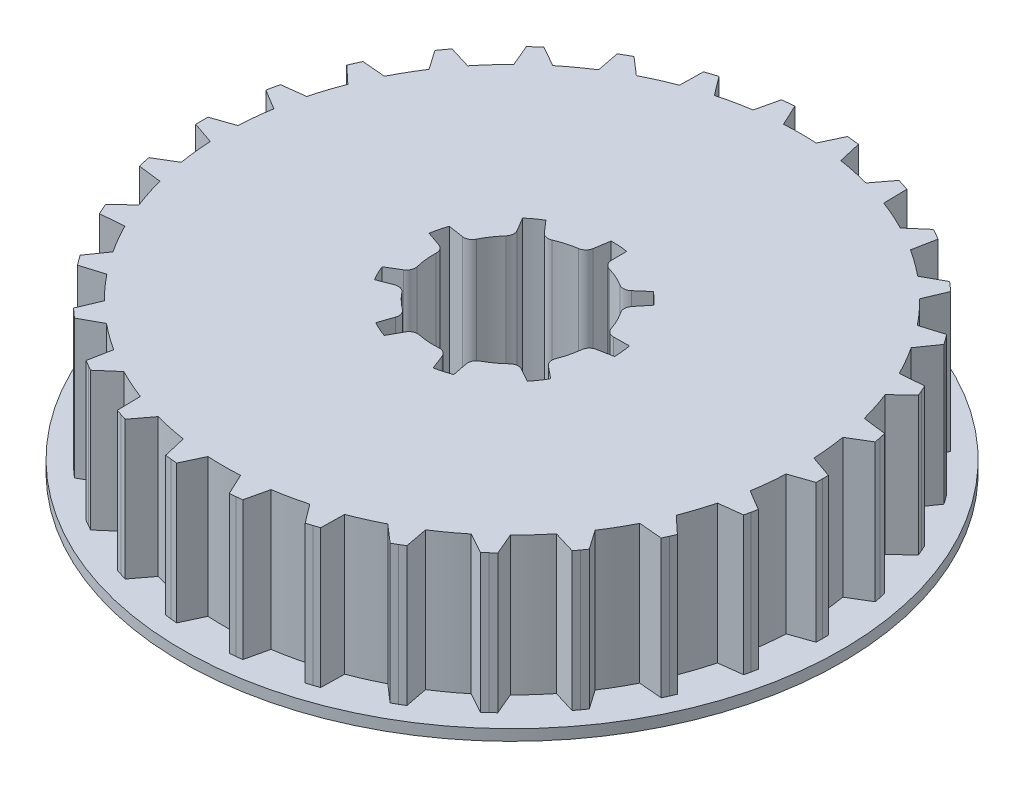
SolidWorks part; units mm, degrees
ref_plane "Front Plane" through (0, 0, 0) normal (0, 0, 1) x (1, 0, 0)
ref_plane "Top Plane" through (0, 0, 0) normal (0, 1, 0) x (1, 0, 0)
ref_plane "Right Plane" through (0, 0, 0) normal (1, 0, 0) x (0, 0, -1)
sketch "Sketch1" plane through (0, 0, 0) normal (0, 1, 0) x (1, 0, 0)
  circle A0 centre (0, 0) radius 13.12
  dimension "D1" = 26.24
extrude "Boss-Extrude1" add sketch "Sketch1" along normal blind 6.3
sketch "Sketch2" plane through (0, 0, 0) normal (0, -1, 0) x (1, 0, 0)
  line L0 (0, 0) -> (-14.12, 0) construction
  line L1 (-13.1243, 0) -> (-13.1049, -0.6297) construction
  line L2 (-13.1243, 0) -> (-13.1049, 0.6297) construction
  line L3 (-14.12, 0) -> (-14.1172, -0.28)
  line L4 (-14.12, 0) -> (-14.1172, 0.28)
  line L5 (-14.1172, -0.28) -> (-12.5942, -0.8061)
  line L6 (-14.1172, 0.28) -> (-12.5942, 0.8061)
  line L7 (-13.8669, 2.6613) -> (-12.4866, 1.83)
  line L8 (-13.7505, 3.209) -> (-12.1514, 3.407)
  line L9 (-13.8114, 2.9357) -> (-13.8669, 2.6613)
  line L10 (-13.8114, 2.9357) -> (-13.7505, 3.209)
  line L11 (-13.0106, 5.4862) -> (-11.8333, 4.3861)
  line L12 (-12.7828, 5.9978) -> (-11.1775, 5.8589)
  line L13 (-12.8993, 5.7431) -> (-13.0106, 5.4862)
  line L14 (-12.8993, 5.7431) -> (-12.7828, 5.9978)
  line L15 (-11.5856, 8.0714) -> (-10.6628, 6.7505)
  line L16 (-11.2565, 8.5244) -> (-9.7151, 8.0548)
  line L17 (-11.4233, 8.2995) -> (-11.5856, 8.0714)
  line L18 (-11.4233, 8.2995) -> (-11.2565, 8.5244)
  line L19 (-9.6543, 10.3038) -> (-9.0262, 8.8199)
  line L20 (-9.2382, 10.6785) -> (-7.8281, 9.8987)
  line L21 (-9.4481, 10.4932) -> (-9.6543, 10.3038)
  line L22 (-9.4481, 10.4932) -> (-9.2382, 10.6785)
  line L23 (-7.3011, 12.0859) -> (-6.9952, 10.5039)
  line L24 (-6.8161, 12.3659) -> (-5.599, 11.31)
  line L25 (-7.06, 12.2283) -> (-7.3011, 12.0859)
  line L26 (-7.06, 12.2283) -> (-6.8161, 12.3659)
  line L27 (-4.6287, 13.3398) -> (-4.6585, 11.7287)
  line L28 (-4.0962, 13.5128) -> (-3.1252, 12.2269)
  line L29 (-4.3633, 13.4289) -> (-4.6287, 13.3398)
  line L30 (-4.3633, 13.4289) -> (-4.0962, 13.5128)
  line L31 (-1.7541, 14.0106) -> (-2.1181, 12.441)
  line L32 (-1.1972, 14.0692) -> (-0.5148, 12.6095)
  line L33 (-1.4759, 14.0426) -> (-1.7541, 14.0106)
  line L34 (-1.4759, 14.0426) -> (-1.1972, 14.0692)
  line L35 (1.1972, 14.0692) -> (0.5148, 12.6095)
  line L36 (1.7541, 14.0106) -> (2.1181, 12.441)
  line L37 (1.4759, 14.0426) -> (1.1972, 14.0692)
  line L38 (1.4759, 14.0426) -> (1.7541, 14.0106)
  line L39 (4.0962, 13.5128) -> (3.1252, 12.2269)
  line L40 (4.6288, 13.3398) -> (4.6585, 11.7287)
  line L41 (4.3633, 13.4289) -> (4.0962, 13.5128)
  line L42 (4.3633, 13.4289) -> (4.6288, 13.3398)
  line L43 (6.8161, 12.3659) -> (5.599, 11.31)
  line L44 (7.3011, 12.0859) -> (6.9952, 10.5039)
  line L45 (7.06, 12.2283) -> (6.8161, 12.3659)
  line L46 (7.06, 12.2283) -> (7.3011, 12.0859)
  line L47 (9.2382, 10.6785) -> (7.8281, 9.8987)
  line L48 (9.6543, 10.3038) -> (9.0262, 8.82)
  line L49 (9.4481, 10.4932) -> (9.2382, 10.6785)
  line L50 (9.4481, 10.4932) -> (9.6543, 10.3038)
  line L51 (11.2565, 8.5244) -> (9.7151, 8.0549)
  line L52 (11.5857, 8.0714) -> (10.6628, 6.7506)
  line L53 (11.4233, 8.2995) -> (11.2565, 8.5244)
  line L54 (11.4233, 8.2995) -> (11.5857, 8.0714)
  line L55 (12.7828, 5.9978) -> (11.1775, 5.8589)
  line L56 (13.0106, 5.4862) -> (11.8333, 4.3861)
  line L57 (12.8993, 5.7431) -> (12.7828, 5.9978)
  line L58 (12.8993, 5.7431) -> (13.0106, 5.4862)
  line L59 (13.7505, 3.209) -> (12.1514, 3.407)
  line L60 (13.8669, 2.6613) -> (12.4866, 1.83)
  line L61 (13.8114, 2.9357) -> (13.7505, 3.209)
  line L62 (13.8114, 2.9357) -> (13.8669, 2.6613)
  line L63 (14.1172, 0.28) -> (12.5942, 0.8061)
  line L64 (14.1172, -0.28) -> (12.5942, -0.8061)
  line L65 (14.12, 0) -> (14.1172, 0.28)
  line L66 (14.12, 0) -> (14.1172, -0.28)
  line L67 (13.8669, -2.6613) -> (12.4866, -1.83)
  line L68 (13.7505, -3.209) -> (12.1514, -3.407)
  line L69 (13.8114, -2.9357) -> (13.8669, -2.6613)
  line L70 (13.8114, -2.9357) -> (13.7505, -3.209)
  line L71 (13.0106, -5.4862) -> (11.8333, -4.3861)
  line L72 (12.7828, -5.9978) -> (11.1775, -5.8589)
  line L73 (12.8993, -5.7431) -> (13.0106, -5.4862)
  line L74 (12.8993, -5.7431) -> (12.7828, -5.9978)
  line L75 (11.5856, -8.0714) -> (10.6628, -6.7505)
  line L76 (11.2565, -8.5244) -> (9.7151, -8.0548)
  line L77 (11.4233, -8.2995) -> (11.5856, -8.0714)
  line L78 (11.4233, -8.2995) -> (11.2565, -8.5244)
  line L79 (9.6543, -10.3038) -> (9.0262, -8.8199)
  line L80 (9.2382, -10.6785) -> (7.8281, -9.8987)
  line L81 (9.4481, -10.4932) -> (9.6543, -10.3038)
  line L82 (9.4481, -10.4932) -> (9.2382, -10.6785)
  line L83 (7.3011, -12.0859) -> (6.9952, -10.5039)
  line L84 (6.8161, -12.3659) -> (5.599, -11.31)
  line L85 (7.06, -12.2283) -> (7.3011, -12.0859)
  line L86 (7.06, -12.2283) -> (6.8161, -12.3659)
  line L87 (4.6287, -13.3398) -> (4.6585, -11.7287)
  line L88 (4.0962, -13.5128) -> (3.1252, -12.2269)
  line L89 (4.3633, -13.4289) -> (4.6287, -13.3398)
  line L90 (4.3633, -13.4289) -> (4.0962, -13.5128)
  line L91 (1.7541, -14.0106) -> (2.1181, -12.441)
  line L92 (1.1972, -14.0692) -> (0.5148, -12.6095)
  line L93 (1.4759, -14.0426) -> (1.7541, -14.0106)
  line L94 (1.4759, -14.0426) -> (1.1972, -14.0692)
  line L95 (-1.1972, -14.0692) -> (-0.5148, -12.6095)
  line L96 (-1.7541, -14.0106) -> (-2.1181, -12.441)
  line L97 (-1.4759, -14.0426) -> (-1.1972, -14.0692)
  line L98 (-1.4759, -14.0426) -> (-1.7541, -14.0106)
  line L99 (-4.0962, -13.5128) -> (-3.1252, -12.2269)
  line L100 (-4.6288, -13.3398) -> (-4.6585, -11.7287)
  line L101 (-4.3633, -13.4289) -> (-4.0962, -13.5128)
  line L102 (-4.3633, -13.4289) -> (-4.6288, -13.3398)
  line L103 (-6.8161, -12.3659) -> (-5.599, -11.31)
  line L104 (-7.3011, -12.0859) -> (-6.9952, -10.5039)
  line L105 (-7.06, -12.2283) -> (-6.8161, -12.3659)
  line L106 (-7.06, -12.2283) -> (-7.3011, -12.0859)
  line L107 (-9.2382, -10.6785) -> (-7.8281, -9.8987)
  line L108 (-9.6543, -10.3038) -> (-9.0262, -8.82)
  line L109 (-9.4481, -10.4932) -> (-9.2382, -10.6785)
  line L110 (-9.4481, -10.4932) -> (-9.6543, -10.3038)
  line L111 (-11.2565, -8.5244) -> (-9.7151, -8.0549)
  line L112 (-11.5857, -8.0714) -> (-10.6628, -6.7506)
  line L113 (-11.4233, -8.2995) -> (-11.2565, -8.5244)
  line L114 (-11.4233, -8.2995) -> (-11.5857, -8.0714)
  line L115 (-12.7828, -5.9978) -> (-11.1775, -5.8589)
  line L116 (-13.0106, -5.4862) -> (-11.8333, -4.3861)
  line L117 (-12.8993, -5.7431) -> (-12.7828, -5.9978)
  line L118 (-12.8993, -5.7431) -> (-13.0106, -5.4862)
  line L119 (-13.7505, -3.209) -> (-12.1514, -3.407)
  line L120 (-13.8669, -2.6613) -> (-12.4866, -1.83)
  line L121 (-13.8114, -2.9357) -> (-13.7505, -3.209)
  line L122 (-13.8114, -2.9357) -> (-13.8669, -2.6613)
  circle A0 centre (0, 0) radius 13.12 construction
  arc A1 (-12.5942, 0.8061) -> (-12.5942, -0.8061) centre (0, 0) ccw
  arc A2 (-12.1514, 3.407) -> (-12.4866, 1.83) centre (0, 0) ccw
  arc A4 (-11.1775, 5.8589) -> (-11.8333, 4.3861) centre (0, 0) ccw
  arc A6 (-9.7151, 8.0548) -> (-10.6628, 6.7505) centre (0, 0) ccw
  arc A7 (-7.8281, 9.8987) -> (-9.0262, 8.8199) centre (0, 0) ccw
  arc A8 (-5.599, 11.31) -> (-6.9952, 10.5039) centre (0, 0) ccw
  arc A9 (-3.1252, 12.2269) -> (-4.6585, 11.7287) centre (0, 0) ccw
  arc A10 (-0.5148, 12.6095) -> (-2.1181, 12.441) centre (0, 0) ccw
  arc A11 (2.1181, 12.441) -> (0.5148, 12.6095) centre (0, 0) ccw
  arc A12 (4.6585, 11.7287) -> (3.1252, 12.2269) centre (0, 0) ccw
  arc A13 (6.9952, 10.5039) -> (5.599, 11.31) centre (0, 0) ccw
  arc A14 (9.0262, 8.82) -> (7.8281, 9.8987) centre (0, 0) ccw
  arc A15 (10.6628, 6.7506) -> (9.7151, 8.0549) centre (0, 0) ccw
  arc A16 (11.8333, 4.3861) -> (11.1775, 5.8589) centre (0, 0) ccw
  arc A17 (12.4866, 1.83) -> (12.1514, 3.407) centre (0, 0) ccw
  arc A18 (12.5942, -0.8061) -> (12.5942, 0.8061) centre (0, 0) ccw
  arc A19 (12.1514, -3.407) -> (12.4866, -1.83) centre (0, 0) ccw
  arc A20 (11.1775, -5.8589) -> (11.8333, -4.3861) centre (0, 0) ccw
  arc A21 (9.7151, -8.0548) -> (10.6628, -6.7505) centre (0, 0) ccw
  arc A22 (7.8281, -9.8987) -> (9.0262, -8.8199) centre (0, 0) ccw
  arc A23 (5.599, -11.31) -> (6.9952, -10.5039) centre (0, 0) ccw
  arc A24 (3.1252, -12.2269) -> (4.6585, -11.7287) centre (0, 0) ccw
  arc A25 (0.5148, -12.6095) -> (2.1181, -12.441) centre (0, 0) ccw
  arc A26 (-2.1181, -12.441) -> (-0.5148, -12.6095) centre (0, 0) ccw
  arc A27 (-4.6585, -11.7287) -> (-3.1252, -12.2269) centre (0, 0) ccw
  arc A28 (-6.9952, -10.5039) -> (-5.599, -11.31) centre (0, 0) ccw
  arc A29 (-9.0262, -8.82) -> (-7.8281, -9.8987) centre (0, 0) ccw
  arc A30 (-10.6628, -6.7506) -> (-9.7151, -8.0549) centre (0, 0) ccw
  arc A31 (-11.8333, -4.3861) -> (-11.1775, -5.8589) centre (0, 0) ccw
  arc A32 (-12.4866, -1.83) -> (-12.1514, -3.407) centre (0, 0) ccw
  point P159 (0, 0)
  dimension "D3" = 0.63
  dimension "D4" = 0.63
  dimension "D5" = 0.28
  dimension "D6" = 0.28
  dimension "D1" = 30
extrude "Boss-Extrude2" add sketch "Sketch2" against normal up to surface (6.3 mm away) up to face at (0, 6.3, 13.12)
sketch "Sketch3" plane through (0, 6.3, 0) normal (0, 1, 0) x (1, 0, 0)
  line L18 (-3.9264, -2.3384) -> (-3.2619, -2.0833)
  line L19 (-1.9682, -3.3326) -> (-2.2, -4.0056)
  line L20 (-1.5047, -4.3152) -> (-1.1596, -3.6926)
  line L21 (0.6344, -3.8181) -> (0.8895, -4.4826)
  line L22 (1.6211, -4.2728) -> (1.4853, -3.5741)
  line L23 (2.9402, -2.517) -> (3.5627, -2.8621)
  line L24 (3.9883, -2.2311) -> (3.4352, -1.7832)
  line L25 (3.8702, -0.0383) -> (4.569, 0.0976)
  line L26 (4.4894, 0.8545) -> (3.7777, 0.8421)
  line L27 (2.9894, 2.4584) -> (3.4373, 3.0116)
  line L28 (2.8898, 3.5403) -> (2.3526, 3.0733)
  line L29 (0.7097, 3.8048) -> (0.6973, 4.5165)
  line L30 (-0.0619, 4.5696) -> (-0.1733, 3.8665)
  line L31 (-1.902, 3.3708) -> (-2.369, 3.9081)
  line L32 (-2.9847, 3.4607) -> (-2.6181, 2.8505)
  line L33 (-3.6237, 1.3596) -> (-4.3268, 1.471)
  line L34 (-4.5109, 0.7325) -> (-3.8379, 0.5007)
  line L35 (-3.6499, -1.2877) -> (-4.26, -1.6544)
  line L36 (-3.9264, -2.3384) -> (-3.2619, -2.0833)
  line L37 (-1.9682, -3.3326) -> (-2.2, -4.0056)
  line L38 (-1.5047, -4.3152) -> (-1.1596, -3.6926)
  line L39 (0.6344, -3.8181) -> (0.8895, -4.4826)
  line L40 (1.6211, -4.2728) -> (1.4853, -3.5741)
  line L41 (2.9402, -2.517) -> (3.5627, -2.8621)
  line L42 (3.9883, -2.2311) -> (3.4352, -1.7832)
  line L43 (3.8702, -0.0383) -> (4.569, 0.0976)
  line L44 (4.4894, 0.8545) -> (3.7777, 0.8421)
  line L45 (2.9894, 2.4584) -> (3.4373, 3.0116)
  line L46 (2.8898, 3.5403) -> (2.3526, 3.0733)
  line L47 (0.7097, 3.8048) -> (0.6973, 4.5165)
  line L48 (-0.0619, 4.5696) -> (-0.1733, 3.8665)
  line L49 (-1.902, 3.3708) -> (-2.369, 3.9081)
  line L50 (-2.9847, 3.4607) -> (-2.6181, 2.8505)
  line L51 (-3.6237, 1.3596) -> (-4.3268, 1.471)
  line L52 (-4.5109, 0.7325) -> (-3.8379, 0.5007)
  line L53 (-3.6499, -1.2877) -> (-4.26, -1.6544)
  arc A47 (-2.8043, -2.2092) -> (-3.2619, -2.0833) centre (-3.1185, -2.4568) ccw
  arc A48 (-2.8043, -2.2092) -> (-2.11, -2.8797) centre (0, 0) ccw
  arc A49 (-1.9682, -3.3326) -> (-2.11, -2.8797) centre (-2.3464, -3.2024) ccw
  arc A50 (-2.2, -4.0056) -> (-1.5047, -4.3152) centre (0, 0) ccw
  arc A51 (-0.7281, -3.495) -> (-1.1596, -3.6926) centre (-0.8097, -3.8865) ccw
  arc A52 (-0.7281, -3.495) -> (0.2347, -3.5623) centre (0, 0) ccw
  arc A53 (0.6344, -3.8181) -> (0.2347, -3.5623) centre (0.261, -3.9614) ccw
  arc A54 (0.8895, -4.4826) -> (1.6211, -4.2728) centre (0, 0) ccw
  arc A55 (1.6887, -3.1453) -> (1.4853, -3.5741) centre (1.8779, -3.4978) ccw
  arc A56 (1.6887, -3.1453) -> (2.4695, -2.578) centre (0, 0) ccw
  arc A57 (2.9402, -2.517) -> (2.4695, -2.578) centre (2.7462, -2.8669) ccw
  arc A58 (3.5627, -2.8621) -> (3.9883, -2.2311) centre (0, 0) ccw
  arc A59 (3.3154, -1.324) -> (3.4352, -1.7832) centre (3.6869, -1.4723) ccw
  arc A60 (3.3154, -1.324) -> (3.5489, -0.3875) centre (0, 0) ccw
  arc A61 (3.8702, -0.0383) -> (3.5489, -0.3875) centre (3.9465, -0.4309) ccw
  arc A62 (4.569, 0.0976) -> (4.4894, 0.8545) centre (0, 0) ccw
  arc A63 (3.3908, 1.1169) -> (3.7777, 0.8421) centre (3.7707, 1.242) ccw
  arc A64 (3.3908, 1.1169) -> (2.9677, 1.9844) centre (0, 0) ccw
  arc A65 (2.9894, 2.4584) -> (2.9677, 1.9844) centre (3.3002, 2.2067) ccw
  arc A66 (3.4373, 3.0116) -> (2.8898, 3.5403) centre (0, 0) ccw
  arc A67 (1.8796, 3.0351) -> (2.3526, 3.0733) centre (2.0902, 3.3752) ccw
  arc A68 (1.8796, 3.0351) -> (0.9979, 3.4277) centre (0, 0) ccw
  arc A69 (0.7097, 3.8048) -> (0.9979, 3.4277) centre (1.1097, 3.8118) ccw
  arc A70 (0.6973, 4.5165) -> (-0.0619, 4.5696) centre (0, 0) ccw
  arc A71 (-0.5111, 3.5332) -> (-0.1733, 3.8665) centre (-0.5684, 3.9291) ccw
  arc A72 (-0.5111, 3.5332) -> (-1.4389, 3.2672) centre (0, 0) ccw
  arc A73 (-1.902, 3.3708) -> (-1.4389, 3.2672) centre (-1.6001, 3.6333) ccw
  arc A74 (-2.369, 3.9081) -> (-2.9847, 3.4607) centre (0, 0) ccw
  arc A75 (-2.6626, 2.3781) -> (-2.6181, 2.8505) centre (-2.961, 2.6445) ccw
  arc A76 (-2.6626, 2.3781) -> (-3.2024, 1.5779) centre (0, 0) ccw
  arc A77 (-3.6237, 1.3596) -> (-3.2024, 1.5779) centre (-3.5612, 1.7547) ccw
  arc A78 (-4.3268, 1.471) -> (-4.5109, 0.7325) centre (0, 0) ccw
  arc A79 (-3.5683, 0.1102) -> (-3.8379, 0.5007) centre (-3.9681, 0.1225) ccw
  arc A80 (-3.5683, 0.1102) -> (-3.4674, -0.8497) centre (0, 0) ccw
  arc A81 (-3.6499, -1.2877) -> (-3.4674, -0.8497) centre (-3.8559, -0.9449) ccw
  arc A82 (-4.26, -1.6544) -> (-3.9264, -2.3384) centre (0, 0) ccw
  arc A83 (-2.8043, -2.2092) -> (-3.2619, -2.0833) centre (-3.1185, -2.4568) ccw
  arc A84 (-2.8043, -2.2092) -> (-2.11, -2.8797) centre (0, 0) ccw
  arc A85 (-1.9682, -3.3326) -> (-2.11, -2.8797) centre (-2.3464, -3.2024) ccw
  arc A86 (-2.2, -4.0056) -> (-1.5047, -4.3152) centre (0, 0) ccw
  arc A87 (-0.7281, -3.495) -> (-1.1596, -3.6926) centre (-0.8097, -3.8865) ccw
  arc A88 (-0.7281, -3.495) -> (0.2347, -3.5623) centre (0, 0) ccw
  arc A89 (0.6344, -3.8181) -> (0.2347, -3.5623) centre (0.261, -3.9614) ccw
  arc A90 (0.8895, -4.4826) -> (1.6211, -4.2728) centre (0, 0) ccw
  arc A91 (1.6887, -3.1453) -> (1.4853, -3.5741) centre (1.8779, -3.4978) ccw
  arc A92 (1.6887, -3.1453) -> (2.4695, -2.578) centre (0, 0) ccw
  arc A93 (2.9402, -2.517) -> (2.4695, -2.578) centre (2.7462, -2.8669) ccw
  arc A94 (3.5627, -2.8621) -> (3.9883, -2.2311) centre (0, 0) ccw
  arc A95 (3.3154, -1.324) -> (3.4352, -1.7832) centre (3.6869, -1.4723) ccw
  arc A96 (3.3154, -1.324) -> (3.5489, -0.3875) centre (0, 0) ccw
  arc A97 (3.8702, -0.0383) -> (3.5489, -0.3875) centre (3.9465, -0.4309) ccw
  arc A98 (4.569, 0.0976) -> (4.4894, 0.8545) centre (0, 0) ccw
  arc A99 (3.3908, 1.1169) -> (3.7777, 0.8421) centre (3.7707, 1.242) ccw
  arc A100 (3.3908, 1.1169) -> (2.9677, 1.9844) centre (0, 0) ccw
  arc A101 (2.9894, 2.4584) -> (2.9677, 1.9844) centre (3.3002, 2.2067) ccw
  arc A102 (3.4373, 3.0116) -> (2.8898, 3.5403) centre (0, 0) ccw
  arc A103 (1.8796, 3.0351) -> (2.3526, 3.0733) centre (2.0902, 3.3752) ccw
  arc A104 (1.8796, 3.0351) -> (0.9979, 3.4277) centre (0, 0) ccw
  arc A105 (0.7097, 3.8048) -> (0.9979, 3.4277) centre (1.1097, 3.8118) ccw
  arc A106 (0.6973, 4.5165) -> (-0.0619, 4.5696) centre (0, 0) ccw
  arc A107 (-0.5111, 3.5332) -> (-0.1733, 3.8665) centre (-0.5684, 3.9291) ccw
  arc A108 (-0.5111, 3.5332) -> (-1.4389, 3.2672) centre (0, 0) ccw
  arc A109 (-1.902, 3.3708) -> (-1.4389, 3.2672) centre (-1.6001, 3.6333) ccw
  arc A110 (-2.369, 3.9081) -> (-2.9847, 3.4607) centre (0, 0) ccw
  arc A111 (-2.6626, 2.3781) -> (-2.6181, 2.8505) centre (-2.961, 2.6445) ccw
  arc A112 (-2.6626, 2.3781) -> (-3.2024, 1.5779) centre (0, 0) ccw
  arc A113 (-3.6237, 1.3596) -> (-3.2024, 1.5779) centre (-3.5612, 1.7547) ccw
  arc A114 (-4.3268, 1.471) -> (-4.5109, 0.7325) centre (0, 0) ccw
  arc A115 (-3.5683, 0.1102) -> (-3.8379, 0.5007) centre (-3.9681, 0.1225) ccw
  arc A116 (-3.5683, 0.1102) -> (-3.4674, -0.8497) centre (0, 0) ccw
  arc A117 (-3.6499, -1.2877) -> (-3.4674, -0.8497) centre (-3.8559, -0.9449) ccw
  arc A118 (-4.26, -1.6544) -> (-3.9264, -2.3384) centre (0, 0) ccw
  dimension "D1" = 0
extrude "Cut-Extrude1" cut sketch "Sketch3" against normal blind 10
sketch "Sketch4" plane through (0, 0, 0) normal (0, -1, 0) x (1, 0, 0)
  circle A0 centre (0, 0) radius 15
  dimension "D1" = 30
extrude "Boss-Extrude3" add sketch "Sketch4" along normal blind 0.5
sketch "Sketch5" plane through (0, 0, 0) normal (0, 1, 0) x (1, 0, 0)
  line L18 (-3.6499, -1.2877) -> (-4.26, -1.6544)
  line L19 (-3.6499, -1.2877) -> (-4.26, -1.6544)
  line L20 (-3.9264, -2.3384) -> (-3.2619, -2.0833)
  line L21 (-3.9264, -2.3384) -> (-3.2619, -2.0833)
  line L22 (-1.9682, -3.3326) -> (-2.2, -4.0056)
  line L23 (-1.9682, -3.3326) -> (-2.2, -4.0056)
  line L24 (-1.5047, -4.3152) -> (-1.1596, -3.6926)
  line L25 (-1.5047, -4.3152) -> (-1.1596, -3.6926)
  line L26 (0.6344, -3.8181) -> (0.8895, -4.4826)
  line L27 (0.6344, -3.8181) -> (0.8895, -4.4826)
  line L28 (1.6211, -4.2728) -> (1.4853, -3.5741)
  line L29 (1.6211, -4.2728) -> (1.4853, -3.5741)
  line L30 (2.9402, -2.517) -> (3.5627, -2.8621)
  line L31 (2.9402, -2.517) -> (3.5627, -2.8621)
  line L32 (3.9883, -2.2311) -> (3.4352, -1.7832)
  line L33 (3.9883, -2.2311) -> (3.4352, -1.7832)
  line L34 (3.8702, -0.0383) -> (4.569, 0.0976)
  line L35 (3.8702, -0.0383) -> (4.569, 0.0976)
  line L36 (4.4894, 0.8545) -> (3.7777, 0.8421)
  line L37 (4.4894, 0.8545) -> (3.7777, 0.8421)
  line L38 (2.9894, 2.4584) -> (3.4373, 3.0116)
  line L39 (2.9894, 2.4584) -> (3.4373, 3.0116)
  line L60 (2.8898, 3.5403) -> (2.3526, 3.0733)
  line L61 (2.8898, 3.5403) -> (2.3526, 3.0733)
  line L62 (0.7097, 3.8048) -> (0.6973, 4.5165)
  line L63 (0.7097, 3.8048) -> (0.6973, 4.5165)
  line L64 (-0.0619, 4.5696) -> (-0.1733, 3.8665)
  line L65 (-0.0619, 4.5696) -> (-0.1733, 3.8665)
  line L66 (-1.902, 3.3708) -> (-2.369, 3.9081)
  line L67 (-1.902, 3.3708) -> (-2.369, 3.9081)
  line L68 (-2.9847, 3.4607) -> (-2.6181, 2.8505)
  line L69 (-2.9847, 3.4607) -> (-2.6181, 2.8505)
  line L70 (-3.6237, 1.3596) -> (-4.3268, 1.471)
  line L71 (-3.6237, 1.3596) -> (-4.3268, 1.471)
  line L72 (-4.5109, 0.7325) -> (-3.8379, 0.5007)
  line L73 (-4.5109, 0.7325) -> (-3.8379, 0.5007)
  arc A31 (-4.26, -1.6544) -> (-3.9264, -2.3384) centre (0, 0) ccw
  arc A32 (-4.26, -1.6544) -> (-3.9264, -2.3384) centre (0, 0) ccw
  arc A33 (-2.8043, -2.2092) -> (-3.2619, -2.0833) centre (-3.1185, -2.4568) ccw
  arc A34 (-2.8043, -2.2092) -> (-3.2619, -2.0833) centre (-3.1185, -2.4568) ccw
  arc A35 (-2.8043, -2.2092) -> (-2.11, -2.8797) centre (0, 0) ccw
  arc A36 (-2.8043, -2.2092) -> (-2.11, -2.8797) centre (0, 0) ccw
  arc A37 (-1.9682, -3.3326) -> (-2.11, -2.8797) centre (-2.3464, -3.2024) ccw
  arc A38 (-1.9682, -3.3326) -> (-2.11, -2.8797) centre (-2.3464, -3.2024) ccw
  arc A39 (-2.2, -4.0056) -> (-1.5047, -4.3152) centre (0, 0) ccw
  arc A40 (-2.2, -4.0056) -> (-1.5047, -4.3152) centre (0, 0) ccw
  arc A41 (-0.7281, -3.495) -> (-1.1596, -3.6926) centre (-0.8097, -3.8865) ccw
  arc A42 (-0.7281, -3.495) -> (-1.1596, -3.6926) centre (-0.8097, -3.8865) ccw
  arc A43 (-0.7281, -3.495) -> (0.2347, -3.5623) centre (0, 0) ccw
  arc A44 (-0.7281, -3.495) -> (0.2347, -3.5623) centre (0, 0) ccw
  arc A45 (0.6344, -3.8181) -> (0.2347, -3.5623) centre (0.261, -3.9614) ccw
  arc A46 (0.6344, -3.8181) -> (0.2347, -3.5623) centre (0.261, -3.9614) ccw
  arc A47 (0.8895, -4.4826) -> (1.6211, -4.2728) centre (0, 0) ccw
  arc A48 (0.8895, -4.4826) -> (1.6211, -4.2728) centre (0, 0) ccw
  arc A49 (1.6887, -3.1453) -> (1.4853, -3.5741) centre (1.8779, -3.4978) ccw
  arc A50 (1.6887, -3.1453) -> (1.4853, -3.5741) centre (1.8779, -3.4978) ccw
  arc A51 (1.6887, -3.1453) -> (2.4695, -2.578) centre (0, 0) ccw
  arc A52 (1.6887, -3.1453) -> (2.4695, -2.578) centre (0, 0) ccw
  arc A53 (2.9402, -2.517) -> (2.4695, -2.578) centre (2.7462, -2.8669) ccw
  arc A54 (2.9402, -2.517) -> (2.4695, -2.578) centre (2.7462, -2.8669) ccw
  arc A55 (3.5627, -2.8621) -> (3.9883, -2.2311) centre (0, 0) ccw
  arc A56 (3.5627, -2.8621) -> (3.9883, -2.2311) centre (0, 0) ccw
  arc A57 (3.3154, -1.324) -> (3.4352, -1.7832) centre (3.6869, -1.4723) ccw
  arc A58 (3.3154, -1.324) -> (3.4352, -1.7832) centre (3.6869, -1.4723) ccw
  arc A59 (3.3154, -1.324) -> (3.5489, -0.3875) centre (0, 0) ccw
  arc A60 (3.3154, -1.324) -> (3.5489, -0.3875) centre (0, 0) ccw
  arc A96 (3.8702, -0.0383) -> (3.5489, -0.3875) centre (3.9465, -0.4309) ccw
  arc A97 (3.8702, -0.0383) -> (3.5489, -0.3875) centre (3.9465, -0.4309) ccw
  arc A98 (4.569, 0.0976) -> (4.4894, 0.8545) centre (0, 0) ccw
  arc A99 (4.569, 0.0976) -> (4.4894, 0.8545) centre (0, 0) ccw
  arc A100 (3.3908, 1.1169) -> (3.7777, 0.8421) centre (3.7707, 1.242) ccw
  arc A101 (3.3908, 1.1169) -> (3.7777, 0.8421) centre (3.7707, 1.242) ccw
  arc A103 (3.3908, 1.1169) -> (2.9677, 1.9844) centre (0, 0) ccw
  arc A105 (3.3908, 1.1169) -> (2.9677, 1.9844) centre (0, 0) ccw
  arc A107 (2.9894, 2.4584) -> (2.9677, 1.9844) centre (3.3002, 2.2067) ccw
  arc A109 (2.9894, 2.4584) -> (2.9677, 1.9844) centre (3.3002, 2.2067) ccw
  arc A111 (3.4373, 3.0116) -> (2.8898, 3.5403) centre (0, 0) ccw
  arc A113 (3.4373, 3.0116) -> (2.8898, 3.5403) centre (0, 0) ccw
  arc A115 (1.8796, 3.0351) -> (2.3526, 3.0733) centre (2.0902, 3.3752) ccw
  arc A117 (1.8796, 3.0351) -> (2.3526, 3.0733) centre (2.0902, 3.3752) ccw
  arc A119 (1.8796, 3.0351) -> (0.9979, 3.4277) centre (0, 0) ccw
  arc A121 (1.8796, 3.0351) -> (0.9979, 3.4277) centre (0, 0) ccw
  arc A122 (0.7097, 3.8048) -> (0.9979, 3.4277) centre (1.1097, 3.8118) ccw
  arc A123 (0.7097, 3.8048) -> (0.9979, 3.4277) centre (1.1097, 3.8118) ccw
  arc A124 (0.6973, 4.5165) -> (-0.0619, 4.5696) centre (0, 0) ccw
  arc A125 (0.6973, 4.5165) -> (-0.0619, 4.5696) centre (0, 0) ccw
  arc A126 (-0.5111, 3.5332) -> (-0.1733, 3.8665) centre (-0.5684, 3.9291) ccw
  arc A127 (-0.5111, 3.5332) -> (-0.1733, 3.8665) centre (-0.5684, 3.9291) ccw
  arc A128 (-0.5111, 3.5332) -> (-1.4389, 3.2672) centre (0, 0) ccw
  arc A129 (-0.5111, 3.5332) -> (-1.4389, 3.2672) centre (0, 0) ccw
  arc A130 (-1.902, 3.3708) -> (-1.4389, 3.2672) centre (-1.6001, 3.6333) ccw
  arc A131 (-1.902, 3.3708) -> (-1.4389, 3.2672) centre (-1.6001, 3.6333) ccw
  arc A132 (-2.369, 3.9081) -> (-2.9847, 3.4607) centre (0, 0) ccw
  arc A133 (-2.369, 3.9081) -> (-2.9847, 3.4607) centre (0, 0) ccw
  arc A134 (-2.6626, 2.3781) -> (-2.6181, 2.8505) centre (-2.961, 2.6445) ccw
  arc A135 (-2.6626, 2.3781) -> (-2.6181, 2.8505) centre (-2.961, 2.6445) ccw
  arc A136 (-2.6626, 2.3781) -> (-3.2024, 1.5779) centre (0, 0) ccw
  arc A137 (-2.6626, 2.3781) -> (-3.2024, 1.5779) centre (0, 0) ccw
  arc A138 (-3.6237, 1.3596) -> (-3.2024, 1.5779) centre (-3.5612, 1.7547) ccw
  arc A139 (-3.6237, 1.3596) -> (-3.2024, 1.5779) centre (-3.5612, 1.7547) ccw
  arc A140 (-4.3268, 1.471) -> (-4.5109, 0.7325) centre (0, 0) ccw
  arc A141 (-4.3268, 1.471) -> (-4.5109, 0.7325) centre (0, 0) ccw
  arc A142 (-3.5683, 0.1102) -> (-3.8379, 0.5007) centre (-3.9681, 0.1225) ccw
  arc A143 (-3.5683, 0.1102) -> (-3.8379, 0.5007) centre (-3.9681, 0.1225) ccw
  arc A144 (-3.5683, 0.1102) -> (-3.4674, -0.8497) centre (0, 0) ccw
  arc A145 (-3.5683, 0.1102) -> (-3.4674, -0.8497) centre (0, 0) ccw
  arc A146 (-3.6499, -1.2877) -> (-3.4674, -0.8497) centre (-3.8559, -0.9449) ccw
  arc A147 (-3.6499, -1.2877) -> (-3.4674, -0.8497) centre (-3.8559, -0.9449) ccw
  dimension "D1" = 0
extrude "Cut-Extrude2" cut sketch "Sketch5" against normal blind 5.5
